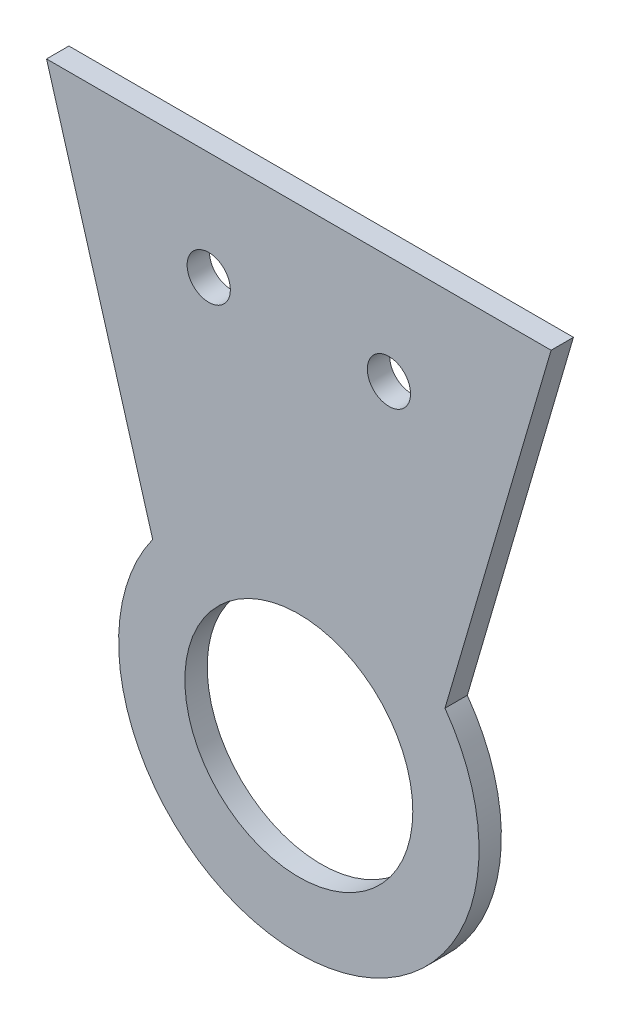
SolidWorks part; units mm, degrees
material "Teak"
ref_plane "Front Plane" through (0, 0, 0) normal (0, 0, 1) x (1, 0, 0)
ref_plane "Top Plane" through (0, 0, 0) normal (0, 1, 0) x (1, 0, 0)
ref_plane "Right Plane" through (0, 0, 0) normal (1, 0, 0) x (0, 0, -1)
sketch "Sketch1" plane through (0, 0, 0) normal (0, 0, 1) x (1, 0, 0)
  line L0 (-35, 65) -> (-35, -35)
  line L1 (-35, 65) -> (35, 65)
  line L2 (-35, -35) -> (35, -35)
  line L3 (35, 65) -> (35, -35)
  line L4 (-35, 65) -> (35, -35) construction
  line L5 (-35, -35) -> (35, 65) construction
  line L6 (0, 0) -> (0, 65) construction
  circle A0 centre (0, 0) radius 15.8115
  circle A2 centre (-12.5, 50) radius 3
  circle A3 centre (12.5, 50) radius 3
  point P4 (0, 15)
  dimension "D1" = 31.623
  dimension "D8" = 6
  dimension "D2" = 35
  dimension "D3" = 70
  dimension "D4" = 0
  dimension "D5" = 100
  dimension "D9" = 15
  dimension "D10" = 25
extrude "Boss-Extrude1" add sketch "Sketch1" along normal blind 3.1
sketch "Sketch2" plane through (0, 0, 3.1) normal (0, 0, 1) x (1, 0, 0)
  line L0 (-35, 65) -> (-16, 0) construction
  line L1 (35, 65) -> (16, 0) construction
  line L2 (-35, 65) -> (0, 65) construction
  line L3 (35, 65) -> (-35, 65) construction
  line L4 (0, 65) -> (0, 0) construction
  line L5 (-35, 65) -> (-20.2752, 14.6258)
  line L6 (20.2752, 14.6258) -> (35, 65)
  arc A0 (-20.2752, 14.6258) -> (20.2752, 14.6258) centre (0, 0) ccw
  dimension "D2" = 25
  dimension "D1" = 32
extrude "Cut-Extrude1" cut sketch "Sketch2" against normal through all and the other way through all flip side to cut
equation "\"thick\" = 3.1mm"
equation "\"small_bearing_outer\"=12.9mm"
equation "\"servo1_L\"=40.7mm"
equation "\"servo1_W\"=20.5mm"
equation "\"servo1_H\"=43.5mm"
equation "\"servo1_hL\"=49mm"
equation "\"servo1_hW\"=10mm"
equation "\"servo1_H2\"=27mm"
equation "\"large_bearing_inner\"=2.75in"
equation "\"large_bearing_outer\"=4.75in"
equation "\"large_bearing_thick\"=3/8in"
equation "\"large_bearing_h1\"=3.25in"
equation "\"large_bearing_h2\"=4.25in"
